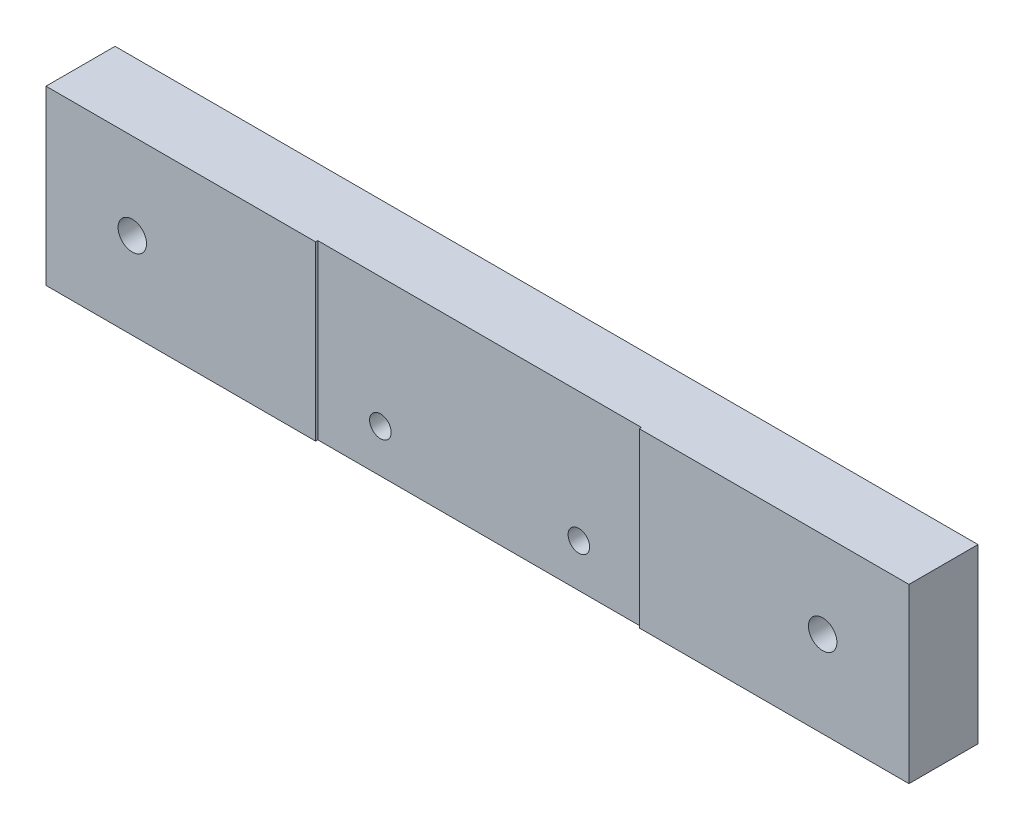
SolidWorks part; units mm, degrees
material "1023 Листовая углеродистая сталь (SS)"
ref_plane "Front" through (0, 0, 0) normal (0, 0, 1) x (1, 0, 0)
ref_plane "Top" through (0, 0, 0) normal (0, 1, 0) x (1, 0, 0)
ref_plane "Right" through (0, 0, 0) normal (1, 0, 0) x (0, 0, -1)
sketch "Sketch1" plane through (0, 0, 0) normal (0, 0, 1) x (1, 0, 0)
  line L1 (-100, 20) -> (100, 20)
  line L2 (-100, 20) -> (-100, -20)
  line L3 (-100, -20) -> (100, -20)
  line L4 (100, 20) -> (100, -20)
  line L5 (-100, 20) -> (100, -20) construction
  line L6 (-100, -20) -> (100, 20) construction
  point P0 (0, 0)
  dimension "D1" = 40
  dimension "D2" = 200
extrude "Extrude1" add sketch "Sketch1" along normal blind 16
sketch "Sketch2" plane through (0, 0, 16) normal (0, 0, -1) x (-1, 0, 0)
  line L1 (-37.5, 20) -> (37.5, 20)
  line L2 (-37.5, 20) -> (-37.5, -20)
  line L3 (-37.5, -20) -> (37.5, -20)
  line L4 (37.5, 20) -> (37.5, -20)
  line L5 (-37.5, 20) -> (37.5, -20) construction
  line L6 (-37.5, -20) -> (37.5, 20) construction
  line L7 (100, -20) -> (-100, -20) construction
  point P0 (0, 0)
  dimension "D1" = 40
  dimension "D2" = 75
extrude "Extrude2" cut sketch "Sketch2" along normal blind 0.5
hole_wizard "M6 Tapped Hole1" positions "Sketch3" profile "Sketch4" tap size "M6" standard "DIN" end condition through all
sketch "Sketch3" plane through (0, 0, 15.5) normal (0, 0, 1) x (1, 0, 0)
  point P0 (-23, -10)
  point P3 (23, -10)
sketch "Sketch4" plane through (-23, -10, 15.5) normal (1, 0, 0) x (0, -1, 0)
  line L0 (0, 0) -> (0, 15.5)
  line L1 (0, 15.5) -> (2.5, 15.5)
  line L2 (2.5, 15.5) -> (2.5, 0)
  line L5 (2.5, 0) -> (0, 0)
  line L11 (0, -6.35) -> (0, 107.95) construction
  dimension "Диаметр проходного сверла" = 5
  dimension "Глубина проходного сверла" = 15.5
cosmetic thread "Cosmetic Thread1"
cosmetic thread "Cosmetic Thread2"
hole_wizard "CBORE for M6 Hex Socket Head Cap Screw1" positions "Sketch5" profile "Sketch6" counterbore size "M6" standard "DIN" end condition through all
sketch "Sketch5" plane through (0, 0, 0) normal (0, 0, -1) x (-1, 0, 0)
  line L0 (80, 0) -> (-80, 0)
  point P0 (-80, 0)
  point P2 (80, 0)
  dimension "D1" = 160
sketch "Sketch6" plane through (80, 0, 0) normal (1, 0, 0) x (0, 1, 0)
  line L0 (0, 0) -> (0, 16)
  line L1 (0, 16) -> (3.3, 16)
  line L3 (3.3, 16) -> (3.3, 6.4)
  line L4 (3.3, 6.4) -> (5.5, 6.4)
  line L5 (5.5, 6.4) -> (5.5, 0)
  line L7 (5.5, 0) -> (0, 0)
  line L11 (0, -6.35) -> (0, 107.95) construction
  dimension "Диаметр сквозного отверстия" = 6.6
  dimension "Глубина сквозного отверстия" = 16
  dimension "Диаметр цековки" = 11
  dimension "Глубина цековки" = 6.4
